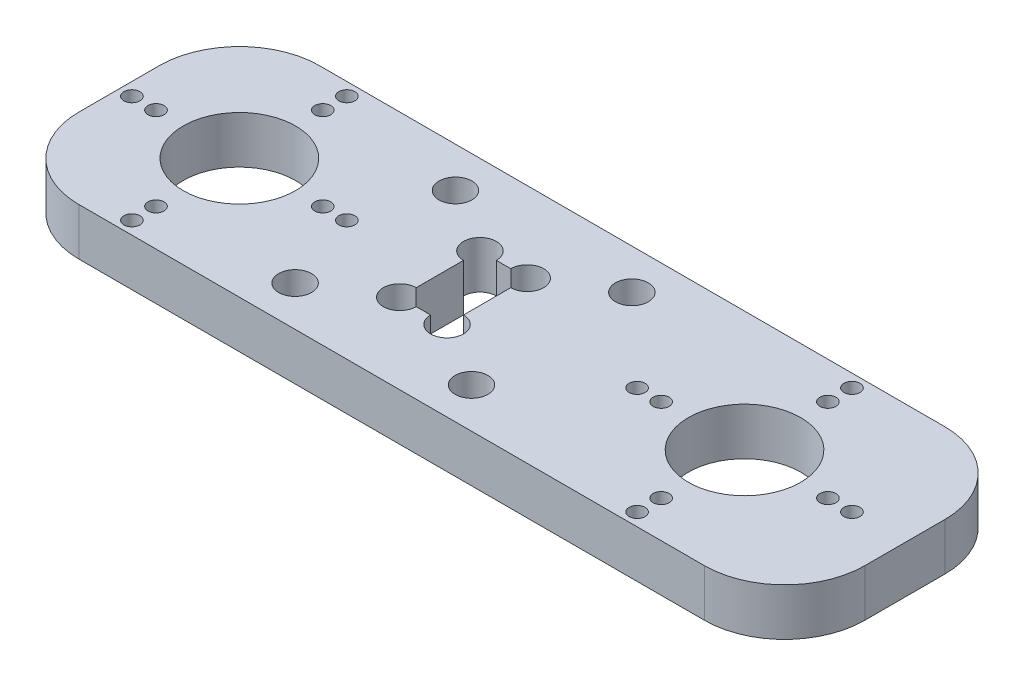
SolidWorks part; units mm, degrees
ref_plane "Front Plane" through (0, 0, 0) normal (0, 0, 1) x (1, 0, 0)
ref_plane "Top Plane" through (0, 0, 0) normal (0, 1, 0) x (1, 0, 0)
ref_plane "Right Plane" through (0, 0, 0) normal (1, 0, 0) x (0, 0, -1)
sketch "Sketch1" plane through (0, 0, 0) normal (0, 1, 0) x (1, 0, 0)
  line L1 (-49, -15) -> (49, -15)
  line L2 (-49, -15) -> (-49, 15)
  line L3 (-49, 15) -> (49, 15)
  line L4 (49, -15) -> (49, 15)
  line L5 (-49, -15) -> (49, 15) construction
  line L6 (-49, 15) -> (49, -15) construction
  circle A0 centre (-34, 0) radius 7
  circle A2 centre (-44.4, 0) radius 1
  circle A9 centre (-47.4, 0) radius 1
  circle A10 centre (-34, 10.4) radius 1
  circle A11 centre (-34, 13.4) radius 1
  circle A12 centre (-23.6, 0) radius 1
  circle A13 centre (-20.6, 0) radius 1
  circle A14 centre (-34, -10.4) radius 1
  circle A15 centre (-34, -13.4) radius 1
  point P0 (0, 0)
  point P26 (-34, 0)
  point P27 (-34, 0)
  dimension "D6" = 14
  dimension "D7" = 15
  dimension "D3" = 10.4
  dimension "D4" = 2
  dimension "D10" = 3
  dimension "D1" = 30
  dimension "D2" = 98
  dimension "D5" = 4
extrude "Boss-Extrude1" add sketch "Sketch1" along normal blind 5.9
sketch "Sketch3" plane through (0, 5.9, 0) normal (0, 1, 0) x (1, 0, 0)
  line L0 (-9, 5) -> (-3.1, 5)
  line L1 (-9, 5) -> (-9, -5)
  line L2 (-9, -5) -> (-3.1, -5)
  line L3 (-3.1, 5) -> (-3.1, -5)
  line L4 (-9, 5) -> (-3.1, -5) construction
  line L5 (-9, -5) -> (-3.1, 5) construction
  line L6 (-49, 15) -> (-49, -15) construction
  point P0 (-6.05, 0)
  dimension "D1" = 5.9
  dimension "D2" = 10
  dimension "D3" = 40
extrude "Cut-Extrude2" cut sketch "Sketch3" against normal blind 10
sketch "Sketch4" plane through (0, 5.9, 0) normal (0, 1, 0) x (1, 0, 0)
  line L0 (49, -15) -> (49, 15) construction
  line L1 (-1.5, -10) -> (39, -10) construction
  line L2 (-1.5, -10) -> (-1.5, 10) construction
  line L3 (-1.5, 10) -> (39, 10) construction
  line L4 (39, -10) -> (39, 10) construction
  line L5 (-1.5, -10) -> (39, 10) construction
  line L6 (-1.5, 10) -> (39, -10) construction
  line L7 (-2.5, 15) -> (-2.5, -15) construction
  line L8 (49, 15) -> (-49, 15) construction
  line L9 (-49, -15) -> (49, -15) construction
  circle A9 centre (-34, 0) radius 7 construction
  circle A10 centre (-34, 0) radius 7
  circle A15 centre (-34, -13.4) radius 1 construction
  circle A16 centre (-34, -10.4) radius 1 construction
  circle A17 centre (-44.4, 0) radius 1 construction
  circle A18 centre (-47.4, 0) radius 1 construction
  circle A19 centre (-34, 13.4) radius 1 construction
  circle A20 centre (-23.6, 0) radius 1 construction
  circle A21 centre (-20.6, 0) radius 1 construction
  circle A22 centre (-34, 10.4) radius 1 construction
  circle A23 centre (-34, -13.4) radius 1
  circle A24 centre (-34, -10.4) radius 1
  circle A25 centre (-44.4, 0) radius 1
  circle A26 centre (-47.4, 0) radius 1
  circle A27 centre (-34, 13.4) radius 1
  circle A28 centre (-23.6, 0) radius 1
  circle A29 centre (-20.6, 0) radius 1
  circle A30 centre (-34, 10.4) radius 1
  circle A31 centre (29, -13.4) radius 1
  circle A32 centre (29, -10.4) radius 1
  circle A33 centre (42.4, 0) radius 1
  circle A34 centre (39.4, 0) radius 1
  circle A35 centre (29, 0) radius 7
  circle A36 centre (29, 10.4) radius 1
  circle A37 centre (29, 13.4) radius 1
  circle A38 centre (18.6, 0) radius 1
  circle A39 centre (15.6, 0) radius 1
  point P0 (18.75, 0)
  point P29 (29, 0)
  dimension "D4" = 10
  dimension "D1" = 40.5
  dimension "D2" = 20
  dimension "D3" = 10
extrude "Cut-Extrude3" cut sketch "Sketch4" against normal blind 10
fillet "Fillet1" radius 10 4 edges at (49, 2.95, 15) (49, 2.95, -15) (-49, 2.95, 15) (-49, 2.95, -15)
sketch "Sketch5" plane through (0, 5.9, 0) normal (0, 1, 0) x (1, 0, 0)
  circle A0 centre (-9, 5) radius 2.05
  circle A1 centre (-3.1, 5) radius 2.05
  circle A2 centre (-3.1, -5) radius 2.05
  circle A3 centre (-9, -5) radius 2.05
  dimension "D1" = 4.1
extrude "Cut-Extrude4" cut sketch "Sketch5" against normal up to next
sketch "Sketch6" plane through (0, 5.9, 0) normal (0, 1, 0) x (1, 0, 0)
  line L0 (0, 0) -> (-49, 0) construction
  line L1 (-49, 5) -> (-49, -5) construction
  line L2 (-17.05, 10) -> (-17.05, -10) construction
  line L4 (39, 15) -> (-39, 15) construction
  line L5 (-6.05, 5) -> (-6.05, 0) construction
  line L6 (-5.15, 5) -> (-6.95, 5) construction
  circle A0 centre (-17.05, 10) radius 2.05
  circle A1 centre (-17.05, -10) radius 2.05
  circle A2 centre (4.95, -10) radius 2.05
  circle A3 centre (4.95, 10) radius 2.05
  point P8 (-17.05, 0)
  dimension "D1" = 5
  dimension "D2" = 4.1
  dimension "D3" = 11
extrude "Cut-Extrude5" cut sketch "Sketch6" against normal blind 10
equation "\"e\" = 5.9"
equation "\"D1@Boss-Extrude1\"=\"e\""
equation "\"D1@Sketch3\"= \"e\""
